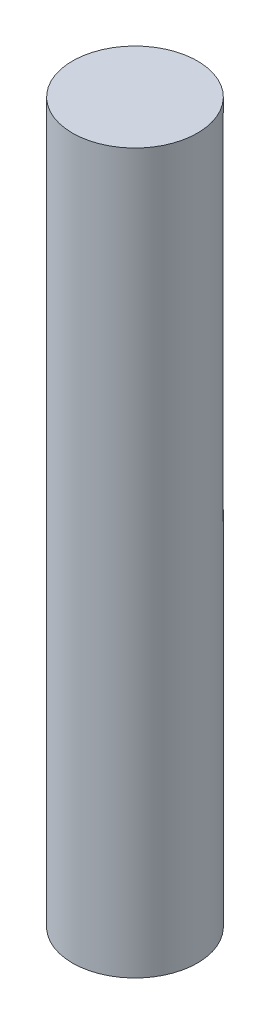
SolidWorks part; units mm, degrees
ref_plane "Front Plane" through (0, 0, 0) normal (0, 0, 1) x (1, 0, 0)
ref_plane "Top Plane" through (0, 0, 0) normal (0, 1, 0) x (1, 0, 0)
ref_plane "Right Plane" through (0, 0, 0) normal (1, 0, 0) x (0, 0, -1)
sketch "Sketch1" plane through (0, 0, 0) normal (0, 1, 0) x (1, 0, 0)
  circle A0 centre (0, 0) radius 8
  dimension "D1" = 16
extrude "Boss-Extrude1" add sketch "Sketch1" along normal blind 46
sketch "Sketch2" plane through (0, 46, 0) normal (0, 1, 0) x (1, 0, 0)
  line L0 (-6.0795, 5.2) -> (6.0795, 5.2)
  circle A0 centre (0, 0) radius 8 construction
  arc A1 (-6.0795, 5.2) -> (6.0795, 5.2) centre (0, 0) ccw
  dimension "D1" = 5.2
extrude "Boss-Extrude2" add sketch "Sketch2" along normal blind 44
sketch "Sketch3" plane through (0, 90, 0) normal (0, 1, 0) x (1, 0, 0)
  circle A0 centre (0, 0) radius 8
  dimension "D1" = 16
extrude "Boss-Extrude3" add sketch "Sketch3" along normal blind 2
